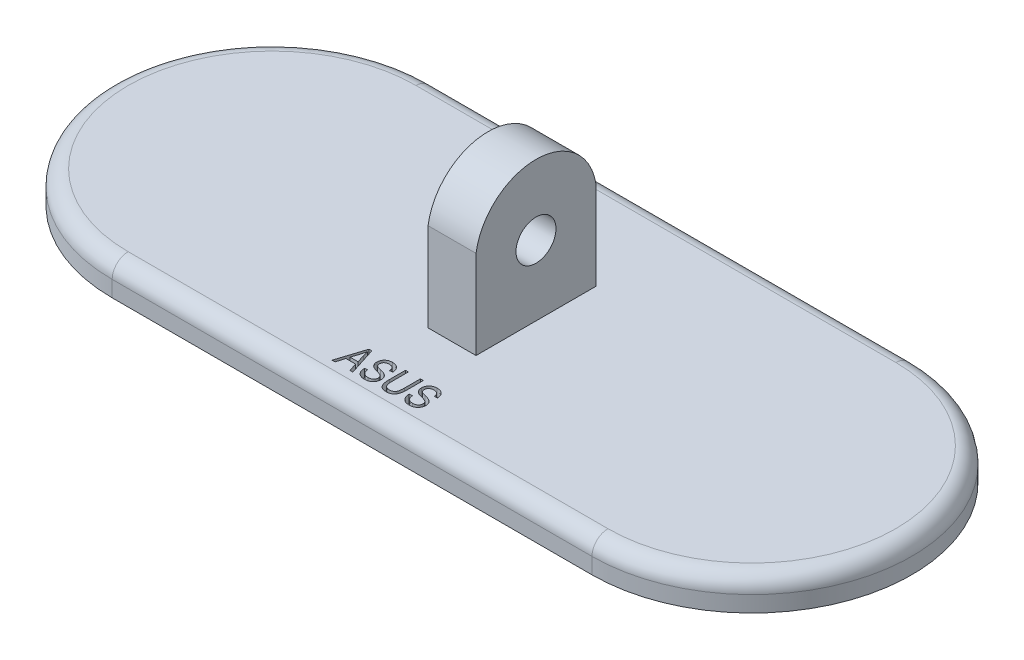
SolidWorks part; units mm, degrees
ref_plane "Front Plane" through (0, 0, 0) normal (0, 0, 1) x (1, 0, 0)
ref_plane "Top Plane" through (0, 0, 0) normal (0, 1, 0) x (1, 0, 0)
ref_plane "Right Plane" through (0, 0, 0) normal (1, 0, 0) x (0, 0, -1)
sketch "Sketch1" plane through (0, 0, 0) normal (0, 1, 0) x (1, 0, 0)
  line L0 (-30, 0) -> (30, 0) construction
  line L1 (-30, 20) -> (30, 20)
  line L2 (-30, -20) -> (30, -20)
  arc A0 (-30, 20) -> (-30, -20) centre (-30, 0) ccw
  arc A1 (30, -20) -> (30, 20) centre (30, 0) ccw
  point P3 (0, 0)
  dimension "D1" = 20
  dimension "D2" = 60
  dimension "D3" = 0
extrude "Boss-Extrude1" add sketch "Sketch1" along normal blind 4
fillet "Fillet1" radius 2 4 edges at (0, 4, -20) (50, 4, 0) (0, 4, 20) (-50, 4, 0)
sketch "Sketch2" plane through (0, 4, 0) normal (0, 1, 0) x (1, 0, 0)
  line L0 (-30, -18) -> (30, -18) construction
  text T0 "ASUS"
  dimension "D1" = 1
  dimension "D2" = 5.5
extrude "Cut-Extrude1" cut sketch "Sketch2" against normal blind 1
sketch "Sketch3" plane through (0, 4, 0) normal (0, 1, 0) x (1, 0, 0)
  line L1 (-3, 7.5) -> (3, 7.5)
  line L2 (-3, 7.5) -> (-3, -7.5)
  line L3 (-3, -7.5) -> (3, -7.5)
  line L4 (3, 7.5) -> (3, -7.5)
  dimension "D1" = 6
  dimension "D2" = 15
  dimension "D3" = 3
  dimension "D4" = 7.5
extrude "Boss-Extrude2" add sketch "Sketch3" along normal blind 17.5
sketch "Sketch4" plane through (-3, 0, 0) normal (-1, 0, 0) x (0, 0, 1)
  line L0 (-7.5, 21.5) -> (-7.5, 4) construction
  line L1 (7.5, 21.5) -> (7.5, 4) construction
  line L2 (-7.5, 12.75) -> (-9.4872, 12.75)
  line L3 (-9.4872, 12.75) -> (-9.4872, 22.792)
  line L4 (-9.4872, 22.792) -> (9.0378, 22.792)
  line L5 (9.0378, 22.792) -> (9.0378, 12.75)
  line L6 (9.0378, 12.75) -> (7.5, 12.75)
  circle A0 centre (0, 12.75) radius 2.5
  arc A1 (-7.5, 12.75) -> (7.5, 12.75) centre (0, 13.9107) cw
  dimension "D1" = 5
  dimension "D2" = 0
extrude "Cut-Extrude2" cut sketch "Sketch4" against normal through all
